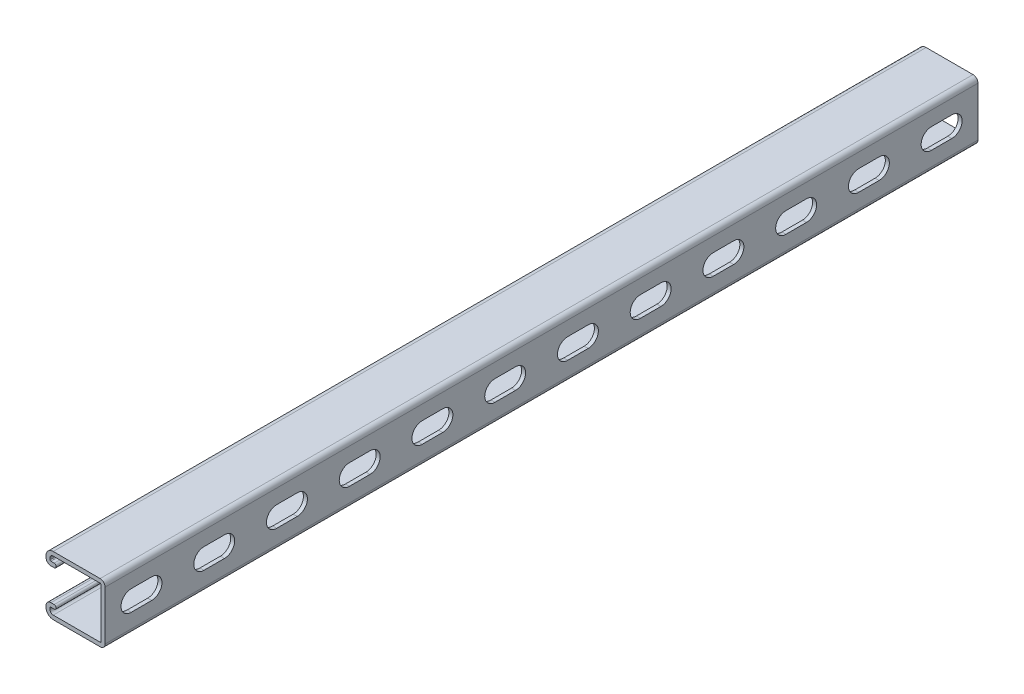
SolidWorks part; units mm, degrees
ref_plane "Front Plane" through (0, 0, 0) normal (0, 0, 1) x (1, 0, 0)
ref_plane "Top Plane" through (0, 0, 0) normal (0, 1, 0) x (1, 0, 0)
ref_plane "Right Plane" through (0, 0, 0) normal (1, 0, 0) x (0, 0, -1)
sketch "Sketch1" plane through (0, 0, 0) normal (0, 0, 1) x (1, 0, 0)
  line L0 (0, 0) -> (-41.275, 0) construction
  line L3 (-41.275, 20.6375) -> (0, 20.6375) construction
  line L4 (-41.275, 20.6375) -> (-41.275, -20.6375) construction
  line L5 (-41.275, -20.6375) -> (0, -20.6375) construction
  line L6 (0, 20.6375) -> (0, -20.6375) construction
  line L7 (-36.2267, 20.6375) -> (-3.4607, 20.6375)
  line L8 (0, 17.1767) -> (0, -17.1767)
  line L9 (-2.794, -17.1767) -> (-2.794, 17.1767)
  line L10 (-3.4608, 17.8435) -> (-36.2267, 17.8435)
  line L11 (-41.275, 15.5892) -> (-41.275, 14.5732)
  line L12 (-37.8142, 11.1125) -> (-35.5346, 11.1125)
  line L14 (-35.5346, 13.9065) -> (-37.8142, 13.9065)
  line L15 (-38.481, 14.5732) -> (-38.481, 15.5892)
  line L16 (-38.481, -14.5733) -> (-38.481, -15.5893)
  line L17 (-35.5346, -13.9065) -> (-37.8142, -13.9065)
  line L18 (-37.8142, -11.1125) -> (-35.5346, -11.1125)
  line L19 (-41.275, -15.5893) -> (-41.275, -14.5733)
  line L20 (-3.4607, -17.8435) -> (-36.2267, -17.8435)
  line L21 (-36.2267, -20.6375) -> (-3.4607, -20.6375)
  line L22 (-2.794, -20.6375) -> (-2.794, 20.6375) construction
  arc A1 (0, 17.1767) -> (-3.4607, 20.6375) centre (-3.4607, 17.1767) ccw
  arc A2 (-2.794, 17.1767) -> (-3.4608, 17.8435) centre (-3.4607, 17.1767) ccw
  arc A4 (-36.2267, 20.6375) -> (-41.275, 15.5892) centre (-36.2267, 15.5892) ccw
  arc A5 (-41.275, 14.5732) -> (-37.8142, 11.1125) centre (-37.8142, 14.5732) ccw
  arc A6 (-35.5346, 11.1125) -> (-35.5346, 13.9065) centre (-35.5346, 12.5095) ccw
  arc A7 (-37.8142, 13.9065) -> (-38.481, 14.5732) centre (-37.8142, 14.5732) cw
  arc A8 (-38.481, 15.5892) -> (-36.2267, 17.8435) centre (-36.2267, 15.5892) cw
  arc A9 (-38.481, -15.5893) -> (-36.2267, -17.8435) centre (-36.2267, -15.5893) ccw
  arc A10 (-37.8142, -13.9065) -> (-38.481, -14.5733) centre (-37.8142, -14.5733) ccw
  arc A11 (-35.5346, -11.1125) -> (-35.5346, -13.9065) centre (-35.5346, -12.5095) cw
  arc A12 (-41.275, -14.5733) -> (-37.8142, -11.1125) centre (-37.8142, -14.5733) cw
  arc A13 (-36.2267, -20.6375) -> (-41.275, -15.5893) centre (-36.2267, -15.5893) cw
  arc A14 (-2.794, -17.1767) -> (-3.4607, -17.8435) centre (-3.4607, -17.1767) cw
  arc A15 (0, -17.1767) -> (-3.4607, -20.6375) centre (-3.4607, -17.1767) cw
  point P24 (0, 20.6375)
  point P65 (-2.794, 0)
  dimension "D1" = 3.4608
  dimension "D2" = 5.0482
  dimension "D3" = 3.4608
  dimension "Ht." = 41.275
  dimension "Wd." = 41.275
  dimension "Thk." = 2.794
  dimension "D4" = 9.525
  dimension "D5" = 7.1374
extrude "Boss-Extrude1" add sketch "Sketch1" against normal blind 609.6
sketch "Sketch3" plane through (0, 0, 0) normal (1, 0, 0) x (0, 0, -1)
  line L0 (0, 0) -> (609.6, 0) construction
  point P2 (101.6, 0)
  point P3 (508, 0)
  dimension "D1" = 101.6
  dimension "D2" = 101.6
  dimension "D3" = 609.6
sketch "Sketch2" plane through (0, 0, 0) normal (1, 0, 0) x (0, 0, -1)
  line L0 (18.2562, 0) -> (32.5437, 0) construction
  line L1 (18.2562, 7.1437) -> (32.5437, 7.1437)
  line L2 (18.2562, -7.1437) -> (32.5437, -7.1437)
  line L3 (18.2562, 0) -> (0, 0) construction
  line L4 (25.4, 0) -> (76.2, 0) construction
  line L5 (0, -17.1767) -> (0, 17.1767) construction
  arc A0 (18.2562, 7.1437) -> (18.2562, -7.1437) centre (18.2562, 0) ccw
  arc A1 (32.5437, -7.1437) -> (32.5437, 7.1437) centre (32.5437, 0) ccw
  point P3 (25.4, 0)
  dimension "Hole to End" = 11.1125
  dimension "D2" = 25.4
extrude "Cut-Extrude1" cut sketch "Sketch2" against normal up to vertex (2.794 mm away) up to point (-2.794, 0, 0)
pattern_linear "LPattern1" count 12 spacing 50.8 along (0, 0, -1) of "Cut-Extrude1"
equation "\"D1@LPattern1\" = \"Slot Ctr.@Sketch2\""
equation "\"Hole Count@LPattern1\" = \"Lg.@Boss-Extrude1\" / \"D1@LPattern1\""
equation "\"D3@Sketch3\" = \"Lg.@Boss-Extrude1\""
